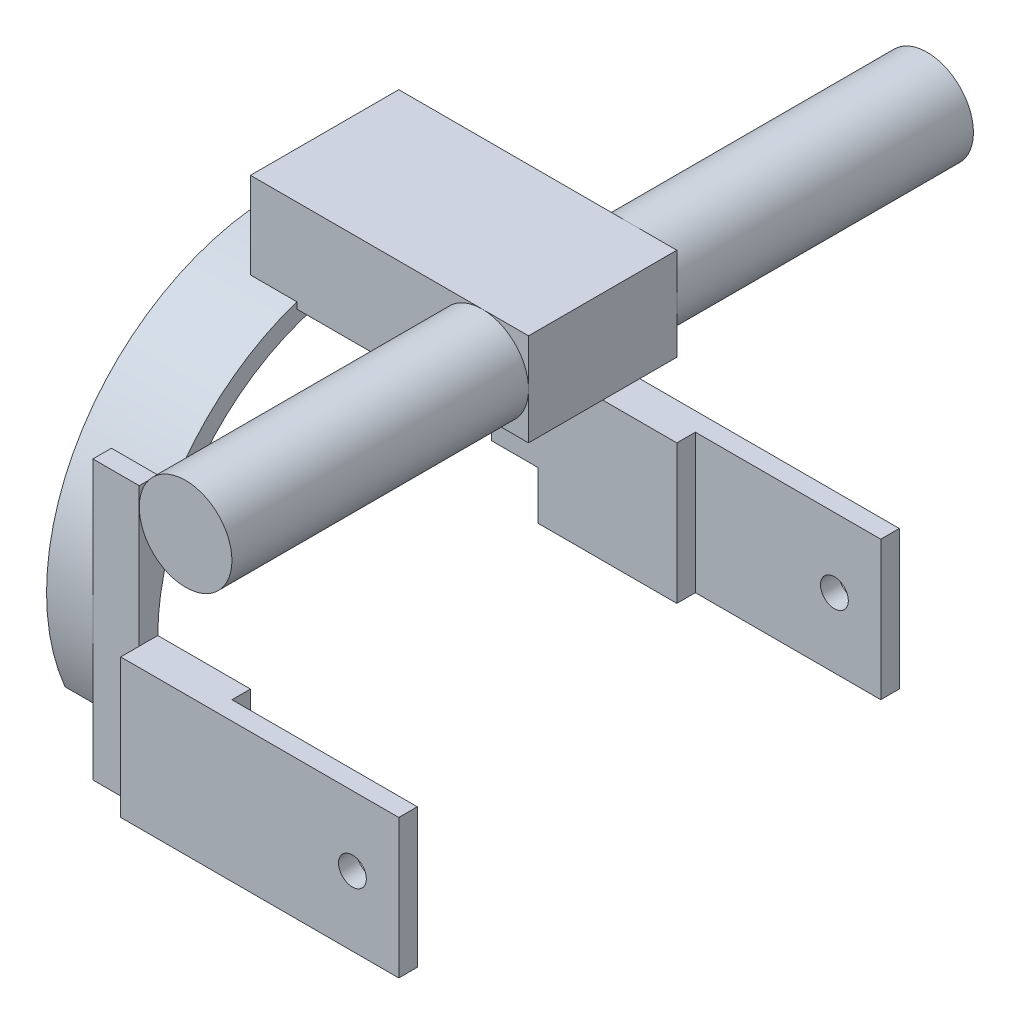
SolidWorks part; units mm, degrees
ref_plane "Front" through (0, 0, 0) normal (0, 0, 1) x (1, 0, 0)
ref_plane "Top" through (0, 0, 0) normal (0, 1, 0) x (1, 0, 0)
ref_plane "Right" through (0, 0, 0) normal (1, 0, 0) x (0, 0, -1)
sketch "草图1" plane through (0, 0, 0) normal (1, 0, 0) x (0, 0, -1)
  line L1 (0, 0) -> (0, 85.9303) construction
  line L2 (-50, 30) -> (-46, 30)
  line L3 (-50, 30) -> (-50, -30)
  line L4 (-50, -30) -> (-46, -30)
  line L5 (-46, 30) -> (-46, 19.5959)
  line L6 (46, 30) -> (50, 30)
  line L7 (46, 30) -> (46, 19.5959)
  line L8 (46, -30) -> (50, -30)
  line L9 (50, 30) -> (50, -30)
  line L10 (-46, 0) -> (-46, -30)
  line L11 (46, 0) -> (46, -30)
  arc A0 (46, 0) -> (-46, 0) centre (0, 0) ccw
  arc A1 (46, 19.5959) -> (-46, 19.5959) centre (0, 0) ccw
  dimension "D1" = 60
  dimension "D2" = 4
  dimension "D4" = 50
  dimension "D5" = 4
  dimension "D6" = 60
extrude "凸台-拉伸1" add sketch "草图1" along normal blind 20
sketch "草图2" plane through (20, 0, 0) normal (1, 0, 0) x (0, 0, -1)
  line L0 (50, -30) -> (50, 30) construction
  line L1 (-50, -30) -> (-46, -30)
  line L2 (-50, -30) -> (-50, 0)
  line L3 (-50, 0) -> (-46, 0)
  line L4 (-46, -30) -> (-46, 0)
  line L5 (46, -30) -> (50, -30)
  line L6 (46, -30) -> (46, 0)
  line L7 (46, 0) -> (50, 0)
  line L8 (50, -30) -> (50, 0)
  dimension "D1" = 30
  dimension "D2" = 30
extrude "凸台-拉伸3" add sketch "草图2" along normal blind 20
sketch "草图4" plane through (0, 0, 0) normal (-1, 0, 0) x (0, 0, 1)
  circle A0 centre (0, 0) radius 50
  circle A1 centre (0, 0) radius 60
extrude "切除-拉伸2" cut sketch "草图4" against normal blind 10
sketch "草图5" plane through (10, 0, 0) normal (-1, 0, 0) x (0, 0, 1)
  line L0 (0, 0) -> (0, 71.1172) construction
  line L1 (0, 46) -> (22.7865, 46) construction
  line L3 (16, 46) -> (-16, 46)
  line L4 (16, 46) -> (16, 66)
  line L5 (16, 66) -> (-16, 66)
  line L6 (-16, 46) -> (-16, 66)
  arc A0 (46, 0) -> (-46, 0) centre (0, 0) ccw construction
  dimension "D1" = 20
  dimension "D2" = 32
  dimension "D3" = 16
extrude "凸台-拉伸4" add sketch "草图5" against normal blind 60
sketch "草图7" plane through (0, 0, 0) normal (0, 0, 1) x (1, 0, 0)
  line L0 (70, 56) -> (-18.9931, 56) construction
  line L1 (70, 46) -> (70, 66) construction
  line L2 (70, 66) -> (70, 46) construction
  circle A0 centre (60, 56) radius 10
  dimension "D1" = 10
extrude "凸台-拉伸5" add sketch "草图7" along normal mid plane 160
sketch "草图9" plane through (0, -30, 0) normal (0, -1, 0) x (1, 0, 0)
  line L1 (20, -50) -> (80, -50)
  line L2 (20, -50) -> (20, -54)
  line L3 (20, -54) -> (80, -54)
  line L4 (80, -50) -> (80, -54)
  line L5 (20, 50) -> (80, 50)
  line L6 (20, 50) -> (20, 54)
  line L7 (20, 54) -> (80, 54)
  line L8 (80, 50) -> (80, 54)
  dimension "D1" = 60
  dimension "D2" = 4
  dimension "D3" = 60
  dimension "D4" = 4
extrude "凸台-拉伸6" add sketch "草图9" against normal blind 30
sketch "草图10" plane through (0, 0, 54) normal (0, 0, 1) x (1, 0, 0)
  circle A0 centre (70, -15) radius 3
extrude "切除-拉伸4" cut sketch "草图10" against normal through all
